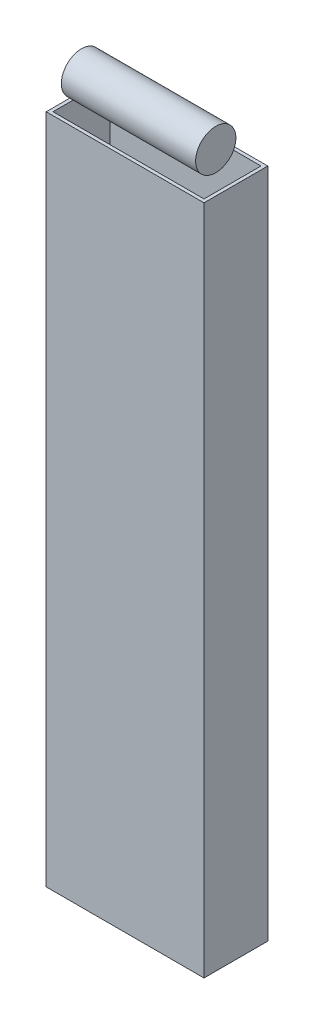
SolidWorks part; units mm, degrees
ref_plane "前视基准面" through (0, 0, 0) normal (0, 0, 1) x (1, 0, 0)
ref_plane "上视基准面" through (0, 0, 0) normal (0, 1, 0) x (1, 0, 0)
ref_plane "右视基准面" through (0, 0, 0) normal (1, 0, 0) x (0, 0, -1)
other "Configuration Table"
sketch "草图1" plane through (0, 0, 0) normal (0, 1, 0) x (1, 0, 0)
  line L0 (22.5, -8.5) -> (22.5, 8.5)
  line L1 (-23.5, -9.5) -> (23.5, -9.5)
  line L2 (-23.5, -9.5) -> (-23.5, 9.5)
  line L3 (-23.5, 9.5) -> (23.5, 9.5)
  line L4 (23.5, -9.5) -> (23.5, 9.5)
  line L5 (-23.5, -9.5) -> (23.5, 9.5) construction
  line L6 (-23.5, 9.5) -> (23.5, -9.5) construction
  line L7 (-22.5, 8.5) -> (22.5, 8.5)
  line L8 (-22.5, -8.5) -> (-22.5, 8.5)
  line L9 (-22.5, -8.5) -> (22.5, -8.5)
  point P0 (0, 0)
  dimension "D1" = 19
  dimension "D2" = 47
  dimension "D3" = 1
extrude "凸台-拉伸1" add sketch "草图1" along normal blind 200
sketch "草图2" plane through (-22.5, 0, 0) normal (1, 0, 0) x (0, 0, -1)
  line L1 (-9.5, 200) -> (9.5, 200) construction
  circle A0 centre (0, 206) radius 6
  point P2 (0, 206.137)
  point P5 (0, 206.4922)
  dimension "D1" = 12
extrude "凸台-拉伸2" add sketch "草图2" along normal blind 40 separate body
